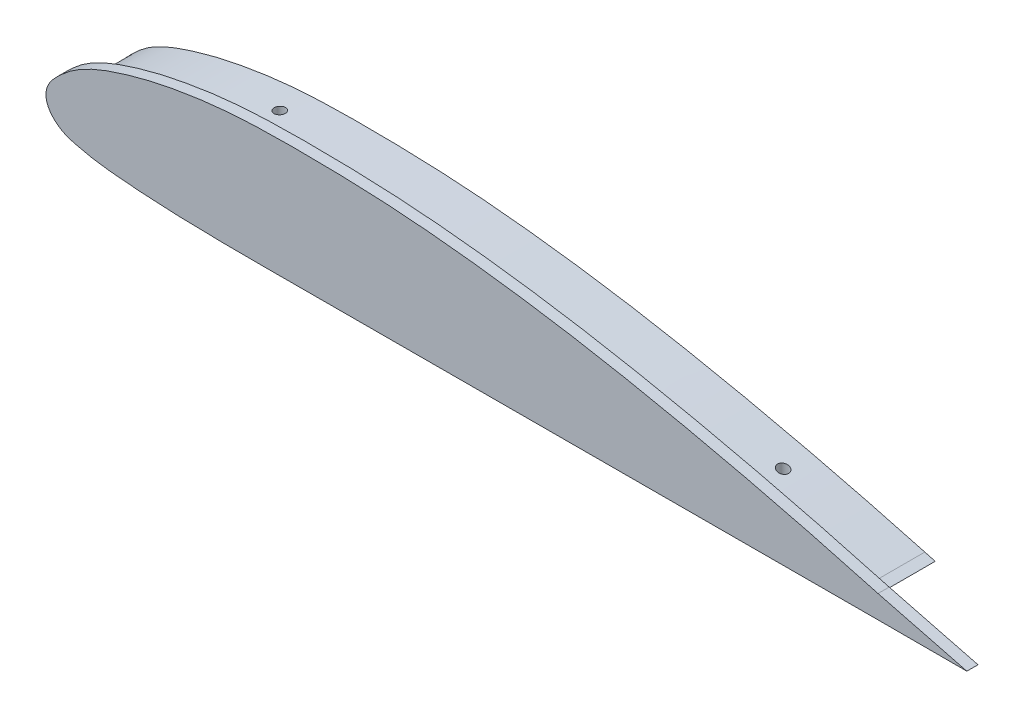
SolidWorks part; units mm, degrees
ref_plane "Front Plane" through (0, 0, 0) normal (0, 0, 1) x (1, 0, 0)
ref_plane "Top Plane" through (0, 0, 0) normal (0, 1, 0) x (1, 0, 0)
ref_plane "Right Plane" through (0, 0, 0) normal (1, 0, 0) x (0, 0, -1)
sketch "Sketch1" plane through (0, 0, 0) normal (0, 0, 1) x (1, 0, 0)
  line L4 (-17.7123, -35.5758) -> (-1.2238, -35.5758)
  line L5 (-1.2238, -35.5758) -> (-17.1809, -31.471)
  spline S2 degree 3 poles (-17.1809, -31.471) (-20.2056, -30.6413) (-26.2535, -28.9879) (-38.4291, -25.8815) (-53.7325, -22.3522) (-72.2469, -18.7478) (-87.8416, -16.5256) (-100.3857, -15.2975) (-109.8486, -14.7321) (-119.2946, -14.543) (-127.1783, -14.5697) (-133.5392, -14.9033) (-138.3167, -15.385) (-143.0523, -16.1027) (-146.9743, -16.888) (-150.0976, -17.6614) (-152.4204, -18.3224) (-154.721, -19.0554) (-157.0283, -19.9018) (-158.9383, -20.7504) (-160.4449, -21.552) (-161.5667, -22.2428) (-162.6439, -23.0198) (-163.6502, -23.8812) (-164.3836, -24.5581) (-165.0259, -25.1979) (-165.5202, -25.7567) (-166.014, -26.4401) (-166.3895, -27.1745) (-166.6066, -27.9625) (-166.6593, -28.6499) (-166.5912, -29.2918) (-166.3998, -29.9297) (-166.1734, -30.4043) (-165.8214, -30.9817) (-165.3347, -31.5618) (-164.7206, -32.1221) (-164.0346, -32.6145) (-163.2893, -33.0085) (-162.336, -33.3878) (-161.2239, -33.6821) (-160.1044, -33.9422) (-158.884, -34.2133) (-157.6571, -34.434) (-156.0223, -34.6701) (-154.0153, -34.8738) (-151.6689, -35.074) (-148.5037, -35.3123) (-144.5593, -35.5212) (-139.8292, -35.6754) (-135.1087, -35.7537) (-130.3968, -35.7823) (-125.692, -35.779) (-119.4312, -35.7563) (-111.6117, -35.7425) (-102.2196, -35.7297) (-92.8302, -35.7113) (-83.4404, -35.6942) (-70.9208, -35.671) (-55.2715, -35.6437) (-36.4921, -35.6094) (-23.9722, -35.5877) (-17.7123, -35.5758) knots 0 0 0 0 0.03125 0.0625 0.125 0.1875 0.25 0.28125 0.3125 0.34375 0.375 0.390625 0.40625 0.421875 0.4375 0.445312 0.453125 0.460938 0.46875 0.476562 0.480469 0.484375 0.488281 0.492188 0.496094 0.498047 0.5 0.501953 0.503906 0.504883 0.505859 0.506836 0.507812 0.508789 0.509766 0.511719 0.513672 0.515625 0.517578 0.519531 0.523438 0.527344 0.53125 0.535156 0.539062 0.546875 0.554688 0.5625 0.578125 0.59375 0.609375 0.625 0.640625 0.65625 0.6875 0.71875 0.75 0.78125 0.8125 0.875 0.9375 1 1 1 1
extrude "Boss-Extrude1" add sketch "Sketch1" along normal blind 2
sketch "Sketch4" plane through (0, 0, 0) normal (0, 0, -1) x (-1, 0, 0)
  line L0 (17.7099, -33.3998) -> (17.7161, -33.5758)
  spline S0 degree 3 poles (-1752.0663, 4617.1234) (-284.9942, -178.3645) (-137.8472, -74.9484) (27.42, -30.7701) (33.2455, -29.2637) (39.0817, -27.8262) (45.8902, -26.2262) (52.6942, -24.7026) (63.3939, -22.5012) (76.0469, -20.2024) (89.7256, -18.3313) (99.5157, -17.3935) (108.3249, -16.8174) (114.2044, -16.6258) (121.0664, -16.5619) (125.9741, -16.5715) (130.8853, -16.7446) (135.8084, -17.114) (139.7519, -17.6021) (144.693, -18.4439) (148.66, -19.3156) (152.605, -20.4616) (155.6094, -21.4769) (158.1057, -22.5462) (160.0998, -23.6553) (161.5146, -24.6573) (162.5844, -25.6177) (163.4024, -26.3911) (163.9246, -26.9592) (164.3139, -27.5109) (164.5291, -27.9473) (164.6657, -28.4647) (164.6332, -28.894) (164.4974, -29.2715) (164.3478, -29.5731) (164.0382, -30.0159) (163.5591, -30.4905) (162.8052, -31.0401) (161.7243, -31.5017) (160.3363, -31.8322) (158.8785, -32.1754) (157.4161, -32.4511) (155.4643, -32.7272) (153.018, -32.9537) (150.0845, -33.1959) (144.2141, -33.5688) (134.4114, -33.8206) (120.6848, -33.7522) (107.9367, -33.7395) (92.2462, -33.7104) (76.5556, -33.6814) (60.8651, -33.653) (50.0778, -33.6346) (41.2519, -33.6178) (32.426, -33.6028) (-377.6366, -32.8236) (-784.7691, -38.6184) (-1180.3743, 4682.5216) knots -1.657819 -1.657819 -1.657819 -1.657819 0.020105 0.030145 0.050191 0.08018 0.090156 0.12002 0.149793 0.199219 0.248396 0.287604 0.297393 0.336535 0.346322 0.365908 0.385531 0.395376 0.415192 0.425184 0.445412 0.455711 0.466191 0.477055 0.482787 0.488946 0.494316 0.497126 0.500187 0.502001 0.50385 0.50502 0.507318 0.507987 0.509024 0.510668 0.513358 0.515716 0.519949 0.524973 0.529954 0.534903 0.539824 0.54963 0.559425 0.569214 0.608356 0.657307 0.706263 0.735637 0.813967 0.862923 0.892297 0.92167 0.951044 0.980418 5.015871 5.015871 5.015871 5.015871 only from (17.7099, -33.3998) to (17.7161, -33.5758) construction
  spline S1 degree 3 poles (17.7099, -33.3998) (19.6519, -32.8671) (22.5636, -32.0683) (27.42, -30.7701) (33.2455, -29.2637) (39.0817, -27.8262) (45.8902, -26.2262) (52.6942, -24.7026) (63.3939, -22.5012) (76.0469, -20.2024) (89.7256, -18.3313) (99.5157, -17.3935) (108.3249, -16.8174) (114.2044, -16.6258) (121.0664, -16.5619) (125.9741, -16.5715) (130.8853, -16.7446) (135.8084, -17.114) (139.7519, -17.6021) (144.693, -18.4439) (148.66, -19.3156) (152.605, -20.4616) (155.6094, -21.4769) (158.1057, -22.5462) (160.0998, -23.6553) (161.5146, -24.6573) (162.5844, -25.6177) (163.4024, -26.3911) (163.9246, -26.9592) (164.3139, -27.5109) (164.5291, -27.9473) (164.6657, -28.4647) (164.6332, -28.894) (164.4974, -29.2715) (164.3478, -29.5731) (164.0382, -30.0159) (163.5591, -30.4905) (162.8052, -31.0401) (161.7243, -31.5017) (160.3363, -31.8322) (158.8785, -32.1754) (157.4161, -32.4511) (155.4643, -32.7272) (153.018, -32.9537) (150.0845, -33.1959) (144.2141, -33.5688) (134.4114, -33.8206) (120.6848, -33.7522) (107.9367, -33.7395) (92.2462, -33.7104) (76.5556, -33.6814) (60.8651, -33.653) (50.0778, -33.6346) (41.2519, -33.6178) (32.426, -33.6028) (24.5807, -33.5879) (19.6774, -33.5795) (17.7161, -33.5758) knots 0 0 0 0 0.020105 0.030145 0.050191 0.08018 0.090156 0.12002 0.149793 0.199219 0.248396 0.287604 0.297393 0.336535 0.346322 0.365908 0.385531 0.395376 0.415192 0.425184 0.445412 0.455711 0.466191 0.477055 0.482787 0.488946 0.494316 0.497126 0.500187 0.502001 0.50385 0.50502 0.507318 0.507987 0.509024 0.510668 0.513358 0.515716 0.519949 0.524973 0.529954 0.534903 0.539824 0.54963 0.559425 0.569214 0.608356 0.657307 0.706263 0.735637 0.813967 0.862923 0.892297 0.92167 0.951044 0.980418 1 1 1 1
extrude "Boss-Extrude2" add sketch "Sketch4" along normal blind 10
sketch "Sketch5" plane through (0, 0, 0) normal (0, 1, 0) x (1, 0, 0)
  line L0 (-17.1809, 0) -> (-166.6394, 0) construction
  circle A0 centre (-131.6394, 5) radius 1
  circle A1 centre (-41.2238, 5) radius 1
  dimension "D1" = 5
extrude "Cut-Extrude1" cut sketch "Sketch5" against normal through all
ref_plane "Plane1" through (0, 0, 12) normal (0, 0, 1) x (1, 0, 0)
sketch "Sketch6" plane through (0, 0, -10) normal (0, 0, -1) x (-1, 0, 0)
  line L2 (1.2238, -35.5758) -> (17.7123, -35.5758)
  line L3 (17.1809, -31.471) -> (1.2238, -35.5758)
  line L4 (1.2238, -35.5758) -> (17.7123, -35.5758)
  line L5 (17.1809, -31.471) -> (1.2238, -35.5758)
  line L6 (18.9126, -33.3281) -> (20.7104, -33.3312)
  line L7 (20.7758, -32.8192) -> (18.9126, -33.3281)
  line L8 (18.9126, -33.3281) -> (20.7104, -33.3312)
  line L9 (20.7758, -32.8192) -> (18.9126, -33.3281)
  spline S1 degree 3 poles (-2153.0812, 2876.623) (-1572.464, -37.7215) (-761.1411, -34.1514) (55.2715, -35.6437) (70.9208, -35.671) (83.4404, -35.6942) (92.8302, -35.7113) (102.2196, -35.7297) (111.6117, -35.7425) (119.4312, -35.7563) (125.692, -35.779) (130.3968, -35.7823) (135.1087, -35.7537) (139.8292, -35.6754) (144.5593, -35.5212) (148.5037, -35.3123) (151.6689, -35.074) (154.0153, -34.8738) (156.0223, -34.6701) (157.6571, -34.434) (158.884, -34.2133) (160.1044, -33.9422) (161.2239, -33.6821) (162.336, -33.3878) (163.2893, -33.0085) (164.0346, -32.6145) (164.7206, -32.1221) (165.3347, -31.5618) (165.8214, -30.9817) (166.1734, -30.4043) (166.3998, -29.9297) (166.5912, -29.2918) (166.6593, -28.6499) (166.6066, -27.9625) (166.3895, -27.1745) (166.014, -26.4401) (165.5202, -25.7567) (165.0259, -25.1979) (164.3836, -24.5581) (163.6502, -23.8812) (162.6439, -23.0198) (161.5667, -22.2428) (160.4449, -21.552) (158.9383, -20.7504) (157.0283, -19.9018) (154.721, -19.0554) (152.4204, -18.3224) (150.0976, -17.6614) (146.9743, -16.888) (143.0523, -16.1027) (138.3167, -15.385) (133.5392, -14.9033) (127.1783, -14.5697) (119.2946, -14.543) (109.8486, -14.7321) (100.3857, -15.2975) (87.8416, -16.5256) (72.2469, -18.7478) (53.7325, -22.3522) (38.4291, -25.8815) (-138.2007, -70.9462) (-277.4971, -193.116) (-2167.8347, 3289.5843) knots -7.963834 -7.963834 -7.963834 -7.963834 0.0625 0.125 0.1875 0.21875 0.25 0.28125 0.3125 0.34375 0.359375 0.375 0.390625 0.40625 0.421875 0.4375 0.445312 0.453125 0.460938 0.464844 0.46875 0.472656 0.476562 0.480469 0.482422 0.484375 0.486328 0.488281 0.490234 0.491211 0.492188 0.493164 0.494141 0.495117 0.496094 0.498047 0.5 0.501953 0.503906 0.507812 0.511719 0.515625 0.519531 0.523438 0.53125 0.539062 0.546875 0.554688 0.5625 0.578125 0.59375 0.609375 0.625 0.65625 0.6875 0.71875 0.75 0.8125 0.875 0.9375 0.96875 2.688371 2.688371 2.688371 2.688371 only from (17.7123, -35.5758) to (17.1809, -31.471)
  spline S2 degree 3 poles (17.7123, -35.5758) (23.9722, -35.5877) (36.4921, -35.6094) (55.2715, -35.6437) (70.9208, -35.671) (83.4404, -35.6942) (92.8302, -35.7113) (102.2196, -35.7297) (111.6117, -35.7425) (119.4312, -35.7563) (125.692, -35.779) (130.3968, -35.7823) (135.1087, -35.7537) (139.8292, -35.6754) (144.5593, -35.5212) (148.5037, -35.3123) (151.6689, -35.074) (154.0153, -34.8738) (156.0223, -34.6701) (157.6571, -34.434) (158.884, -34.2133) (160.1044, -33.9422) (161.2239, -33.6821) (162.336, -33.3878) (163.2893, -33.0085) (164.0346, -32.6145) (164.7206, -32.1221) (165.3347, -31.5618) (165.8214, -30.9817) (166.1734, -30.4043) (166.3998, -29.9297) (166.5912, -29.2918) (166.6593, -28.6499) (166.6066, -27.9625) (166.3895, -27.1745) (166.014, -26.4401) (165.5202, -25.7567) (165.0259, -25.1979) (164.3836, -24.5581) (163.6502, -23.8812) (162.6439, -23.0198) (161.5667, -22.2428) (160.4449, -21.552) (158.9383, -20.7504) (157.0283, -19.9018) (154.721, -19.0554) (152.4204, -18.3224) (150.0976, -17.6614) (146.9743, -16.888) (143.0523, -16.1027) (138.3167, -15.385) (133.5392, -14.9033) (127.1783, -14.5697) (119.2946, -14.543) (109.8486, -14.7321) (100.3857, -15.2975) (87.8416, -16.5256) (72.2469, -18.7478) (53.7325, -22.3522) (38.4291, -25.8815) (26.2535, -28.9879) (20.2056, -30.6413) (17.1809, -31.471) knots 0 0 0 0 0.0625 0.125 0.1875 0.21875 0.25 0.28125 0.3125 0.34375 0.359375 0.375 0.390625 0.40625 0.421875 0.4375 0.445312 0.453125 0.460938 0.464844 0.46875 0.472656 0.476562 0.480469 0.482422 0.484375 0.486328 0.488281 0.490234 0.491211 0.492188 0.493164 0.494141 0.495117 0.496094 0.498047 0.5 0.501953 0.503906 0.507812 0.511719 0.515625 0.519531 0.523438 0.53125 0.539062 0.546875 0.554688 0.5625 0.578125 0.59375 0.609375 0.625 0.65625 0.6875 0.71875 0.75 0.8125 0.875 0.9375 0.96875 1 1 1 1
  spline S3 degree 3 poles (-3436.2373, -1627.6892) (-2305.1312, -28.116) (-1126.802, -31.2687) (57.5062, -33.3974) (75.9041, -33.4302) (91.2357, -33.4581) (103.501, -33.4821) (112.6996, -33.4933) (121.8997, -33.5135) (129.5643, -33.5416) (135.6938, -33.4965) (140.2896, -33.4129) (144.8816, -33.2544) (148.7043, -33.0445) (151.7562, -32.8086) (154.0468, -32.612) (156.3244, -32.3721) (158.2017, -32.0635) (159.6865, -31.7286) (160.8085, -31.4684) (161.8941, -31.1685) (162.8943, -30.7063) (163.7412, -30.0102) (164.3939, -29.124) (164.4205, -28.1315) (163.8227, -27.2022) (163.0533, -26.3936) (162.2102, -25.6147) (161.354, -24.8725) (160.1381, -23.9771) (158.4982, -23.0289) (156.4202, -22.0862) (154.2786, -21.2835) (151.3713, -20.341) (147.6845, -19.3393) (143.1896, -18.415) (138.656, -17.7009) (134.0946, -17.2061) (127.9852, -16.8421) (120.3257, -16.7864) (111.1333, -16.9422) (101.9566, -17.4342) (92.804, -18.2836) (83.678, -19.3955) (71.5573, -21.2159) (56.4987, -24.0757) (-302.6464, -105.0181) (-575.0639, -524.144) (-1267.5985, 3633.4875) knots -11.630495 -11.630495 -11.630495 -11.630495 0.071582 0.132813 0.194043 0.255273 0.285888 0.316503 0.347118 0.377734 0.393041 0.408349 0.423656 0.438964 0.446618 0.454271 0.461925 0.469579 0.473406 0.477233 0.48106 0.484887 0.488713 0.49254 0.496367 0.500194 0.504021 0.507848 0.511675 0.515502 0.523155 0.530809 0.538463 0.546117 0.561424 0.576732 0.592039 0.607347 0.622655 0.65327 0.683885 0.7145 0.745115 0.77573 0.806345 0.867576 0.928806 4.483446 4.483446 4.483446 4.483446 only from (20.7104, -33.3312) to (20.7758, -32.8192)
  spline S4 degree 3 poles (20.7104, -33.3312) (26.843, -33.3421) (39.1083, -33.3643) (57.5062, -33.3974) (75.9041, -33.4302) (91.2357, -33.4581) (103.501, -33.4821) (112.6996, -33.4933) (121.8997, -33.5135) (129.5643, -33.5416) (135.6938, -33.4965) (140.2896, -33.4129) (144.8816, -33.2544) (148.7043, -33.0445) (151.7562, -32.8086) (154.0468, -32.612) (156.3244, -32.3721) (158.2017, -32.0635) (159.6865, -31.7286) (160.8085, -31.4684) (161.8941, -31.1685) (162.8943, -30.7063) (163.7412, -30.0102) (164.3939, -29.124) (164.4205, -28.1315) (163.8227, -27.2022) (163.0533, -26.3936) (162.2102, -25.6147) (161.354, -24.8725) (160.1381, -23.9771) (158.4982, -23.0289) (156.4202, -22.0862) (154.2786, -21.2835) (151.3713, -20.341) (147.6845, -19.3393) (143.1896, -18.415) (138.656, -17.7009) (134.0946, -17.2061) (127.9852, -16.8421) (120.3257, -16.7864) (111.1333, -16.9422) (101.9566, -17.4342) (92.804, -18.2836) (83.678, -19.3955) (71.5573, -21.2159) (56.4987, -24.0757) (38.5575, -28.1192) (26.6893, -31.2044) (20.7758, -32.8192) knots 0.010352 0.010352 0.010352 0.010352 0.071582 0.132813 0.194043 0.255273 0.285888 0.316503 0.347118 0.377734 0.393041 0.408349 0.423656 0.438964 0.446618 0.454271 0.461925 0.469579 0.473406 0.477233 0.48106 0.484887 0.488713 0.49254 0.496367 0.500194 0.504021 0.507848 0.511675 0.515502 0.523155 0.530809 0.538463 0.546117 0.561424 0.576732 0.592039 0.607347 0.622655 0.65327 0.683885 0.7145 0.745115 0.77573 0.806345 0.867576 0.928806 0.990036 0.990036 0.990036 0.990036
  dimension "D1" = 0
  dimension "D2" = 0
extrude "Cut-Extrude2" cut sketch "Sketch6" against normal up to surface (10 mm away) up to face at (-11.9504, -33.5234, 0)
